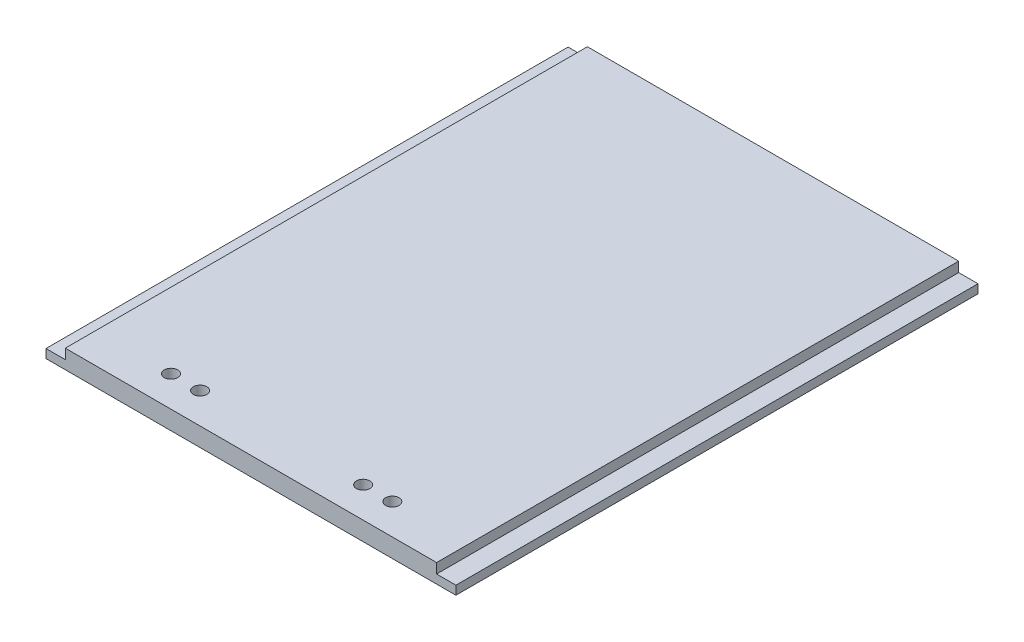
SolidWorks part; units mm, degrees
ref_plane "Front Plane" through (0, 0, 0) normal (0, 0, 1) x (1, 0, 0)
ref_plane "Top Plane" through (0, 0, 0) normal (0, 1, 0) x (1, 0, 0)
ref_plane "Right Plane" through (0, 0, 0) normal (1, 0, 0) x (0, 0, -1)
sketch "Sketch1" plane through (0, 0, 0) normal (0, 1, 0) x (1, 0, 0)
  line L1 (0, 0) -> (139.192, 0)
  line L2 (0, 0) -> (0, 177.292)
  line L3 (0, 177.292) -> (139.192, 177.292)
  line L4 (139.192, 0) -> (139.192, 177.292)
  dimension "D1" = 139.192
  dimension "D2" = 177.292
extrude "Boss-Extrude1" add sketch "Sketch1" along normal blind 6.35
sketch "Sketch2" plane through (0, 6.35, 0) normal (0, 1, 0) x (1, 0, 0)
  line L0 (69.596, 177.292) -> (69.596, 0) construction
  line L1 (139.192, 177.292) -> (0, 177.292) construction
  line L2 (0, 0) -> (139.192, 0) construction
  line L3 (132.642, 177.292) -> (132.642, 0)
  line L4 (0, 177.292) -> (6.55, 177.292)
  line L5 (0, 177.292) -> (0, 0)
  line L6 (0, 0) -> (6.55, 0)
  line L7 (6.55, 177.292) -> (6.55, 0)
  line L8 (139.192, 0) -> (132.642, 0)
  line L9 (139.192, 177.292) -> (139.192, 0)
  line L10 (139.192, 177.292) -> (132.642, 177.292)
  dimension "D1" = 6.55
extrude "Cut-Extrude1" cut sketch "Sketch2" against normal blind 3.375
sketch "Sketch5" plane through (0, 0, 0) normal (0, -1, 0) x (1, 0, 0)
  line L0 (107.188, -8.128) -> (107.188, 0) construction
  line L1 (0, 0) -> (139.192, 0) construction
  line L2 (109.474, -10.414) -> (139.192, -10.414) construction
  line L3 (139.192, 0) -> (139.192, -177.292) construction
  line L4 (104.902, -10.414) -> (99.568, -10.414) construction
  line L5 (39.624, -10.414) -> (34.29, -10.414) construction
  line L7 (94.996, -10.414) -> (44.196, -10.414) construction
  line L8 (29.718, -10.414) -> (0, -10.414) construction
  line L9 (0, -177.292) -> (0, 0) construction
  circle A0 centre (107.188, -10.414) radius 2.286
  circle A1 centre (97.282, -10.414) radius 2.286
  circle A2 centre (41.91, -10.414) radius 2.286
  circle A3 centre (32.004, -10.414) radius 2.286
  dimension "D2" = 4.572
  dimension "D3" = 4.572
  dimension "D4" = 4.572
  dimension "D5" = 4.572
  dimension "D1" = 8.128
  dimension "D6" = 5.334
  dimension "D7" = 5.334
  dimension "D8" = 50.8
extrude "Cut-Extrude3" cut sketch "Sketch5" against normal blind 12.7
